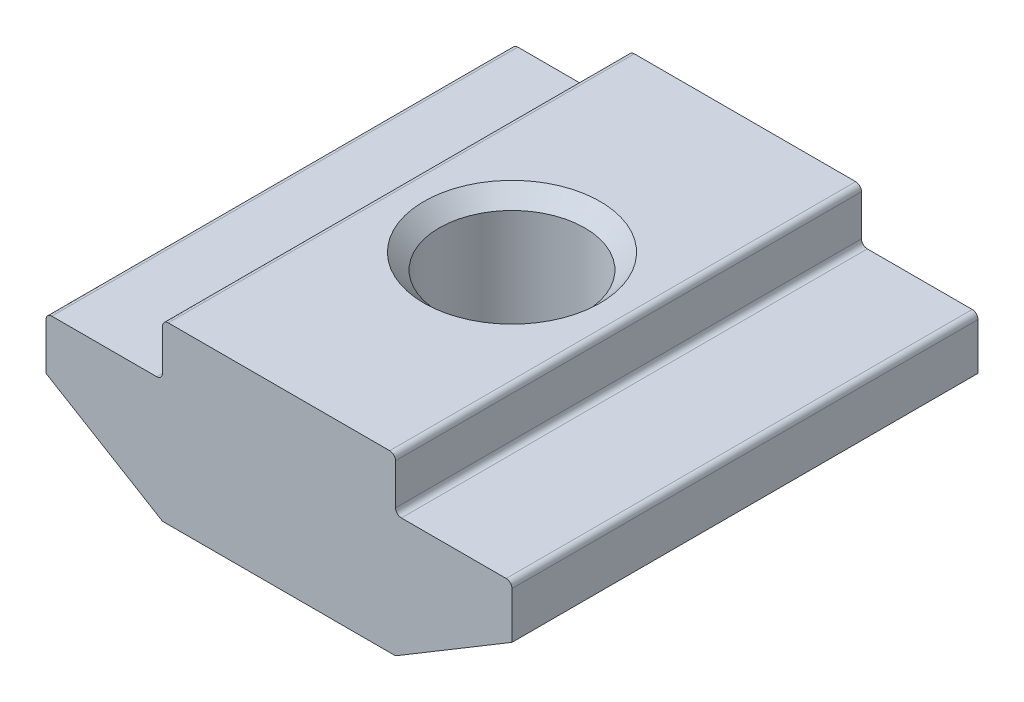
SolidWorks part; units mm, degrees
ref_plane "Спереди" through (0, 0, 0) normal (0, 0, 1) x (1, 0, 0)
ref_plane "Сверху" through (0, 0, 0) normal (0, 1, 0) x (1, 0, 0)
ref_plane "Справа" through (0, 0, 0) normal (1, 0, 0) x (0, 0, -1)
sketch "Эскиз1" plane through (0, 0, 0) normal (0, 0, 1) x (1, 0, 0)
  line L0 (4, 0) -> (-4, 0)
  line L1 (-4, 0) -> (-4, -1.8)
  line L2 (-4, -1.8) -> (-8, -1.8)
  line L3 (-8, -1.8) -> (-8, -3.6)
  line L4 (-8, -3.6) -> (-4, -6)
  line L5 (-4, -6) -> (4, -6)
  line L6 (0, -6) -> (0, 0) construction
  line L7 (8, -3.6) -> (4, -6)
  line L8 (8, -1.8) -> (8, -3.6)
  line L9 (4, -1.8) -> (8, -1.8)
  line L10 (4, 0) -> (4, -1.8)
  point P3 (-4, -0.9)
  point P9 (-2.7421, -5)
  point P10 (-5, -1.6182)
  dimension "D1" = 8
  dimension "D2" = 16
  dimension "D4" = 6
  dimension "D5" = 4.2
extrude "Бобышка-Вытянуть1" add sketch "Эскиз1" along normal mid plane 16
hole_wizard "Отверстие обработанное метчиком M62" positions "Эскиз2" profile "Эскиз4" tap size "M6" standard "ISO" end condition through all
sketch "Эскиз2" plane through (0, 0, 0) normal (0, 1, 0) x (1, 0, 0)
  point P0 (0, 0)
sketch "Эскиз4" plane through (0, 0, 0) normal (1, 0, 0) x (0, 0, 1)
  line L0 (0, 0) -> (0, 6)
  line L1 (0, 6) -> (3.025, 6)
  line L2 (2.5, 5.475) -> (2.5, 0.525)
  line L3 (2.5, 0.525) -> (3.025, 0)
  line L5 (3.025, 0) -> (0, 0)
  line L6 (-2.5, 0.525) -> (-3.025, 0) construction
  line L7 (3.025, 6) -> (2.5, 5.475)
  line L8 (-3.025, 6) -> (-2.5, 5.475) construction
  line L11 (0, -6.35) -> (0, 107.95) construction
  dimension "Диаметр проходного сверла" = 5
  dimension "Глубина проходного сверла" = 6
  dimension "Диаметр передней зенковки" = 6.05
  dimension "Угол передней зенковки" = 90
  dimension "Диаметр задней зенковки" = 6.05
  dimension "Угол задней зенковки" = 90
cosmetic thread "Отверстие резьбы1" parameters "D2"=6
fillet "Скругление1" radius 0.2 8 edges at (4, -6, 0) (-4, -6, 0) (8, -1.8, 0) (4, -1.8, 0) (4, 0, 0) (-4, 0, 0) (-8, -1.8, 0) (-4, -1.8, 0)
